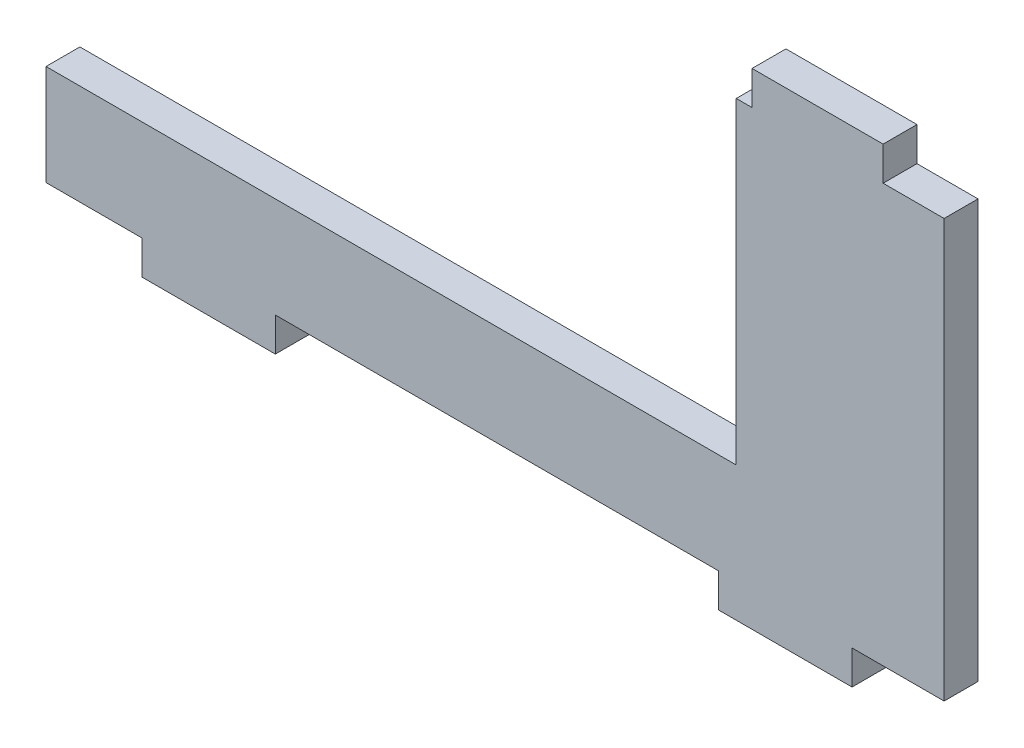
SolidWorks part; units mm, degrees
ref_plane "Alzado" through (0, 0, 0) normal (0, 0, 1) x (1, 0, 0)
ref_plane "Planta" through (0, 0, 0) normal (0, 1, 0) x (1, 0, 0)
ref_plane "Vista lateral" through (0, 0, 0) normal (1, 0, 0) x (0, 0, -1)
sketch "Croquis1" plane through (0, 0, 0) normal (0, 0, 1) x (1, 0, 0)
  line L1 (-39.75, 21.5) -> (39.75, 21.5)
  line L2 (-39.75, 21.5) -> (-39.75, -21.5)
  line L3 (-39.75, -21.5) -> (39.75, -21.5)
  line L4 (39.75, 21.5) -> (39.75, -21.5)
  line L5 (-39.75, 21.5) -> (39.75, -21.5) construction
  line L6 (-39.75, -21.5) -> (39.75, 21.5) construction
  line L7 (-39.75, 21.5) -> (21.35, 21.5)
  line L8 (-39.75, 21.5) -> (-39.75, -9.6)
  line L9 (-39.75, -9.6) -> (21.35, -9.6)
  line L10 (21.35, 21.5) -> (21.35, -9.6)
  line L11 (-39.75, -21.5) -> (-31.25, -21.5)
  line L12 (-39.75, -21.5) -> (-39.75, -18.5)
  line L13 (-39.75, -18.5) -> (-31.25, -18.5)
  line L14 (-31.25, -21.5) -> (-31.25, -18.5)
  line L15 (-19.45, -21.5) -> (19.8, -21.5)
  line L16 (-19.45, -21.5) -> (-19.45, -18.5)
  line L17 (-19.45, -18.5) -> (19.8, -18.5)
  line L18 (19.8, -21.5) -> (19.8, -18.5)
  line L19 (31.6, -21.5) -> (39.75, -21.5)
  line L20 (31.6, -21.5) -> (31.6, -18.5)
  line L21 (31.6, -18.5) -> (39.75, -18.5)
  line L22 (39.75, -21.5) -> (39.75, -18.5)
  line L23 (39.75, 21.5) -> (34.35, 21.5)
  line L24 (39.75, 21.5) -> (39.75, 18.5)
  line L25 (39.75, 18.5) -> (34.35, 18.5)
  line L26 (34.35, 21.5) -> (34.35, 18.5)
  line L27 (21.35, 21.5) -> (22.75, 21.5)
  line L28 (21.35, 21.5) -> (21.35, 18.5)
  line L29 (21.35, 18.5) -> (22.75, 18.5)
  line L30 (22.75, 21.5) -> (22.75, 18.5)
  point P0 (0, 0)
  dimension "D1" = 79.5
  dimension "D2" = 43
  dimension "D3" = 18.4
  dimension "D4" = 11.9
  dimension "D5" = 8.9
  dimension "D6" = 8.5
  dimension "D7" = 11.8
  dimension "D8" = 39.25
  dimension "D9" = 11.8
  dimension "D10" = 5.4
  dimension "D11" = 3
  dimension "D12" = 11.6
  dimension "D13" = 37
extrude "Saliente-Extruir1" add sketch "Croquis1" along normal blind 3 contours L1 L10 L9 L2 L3 L4
